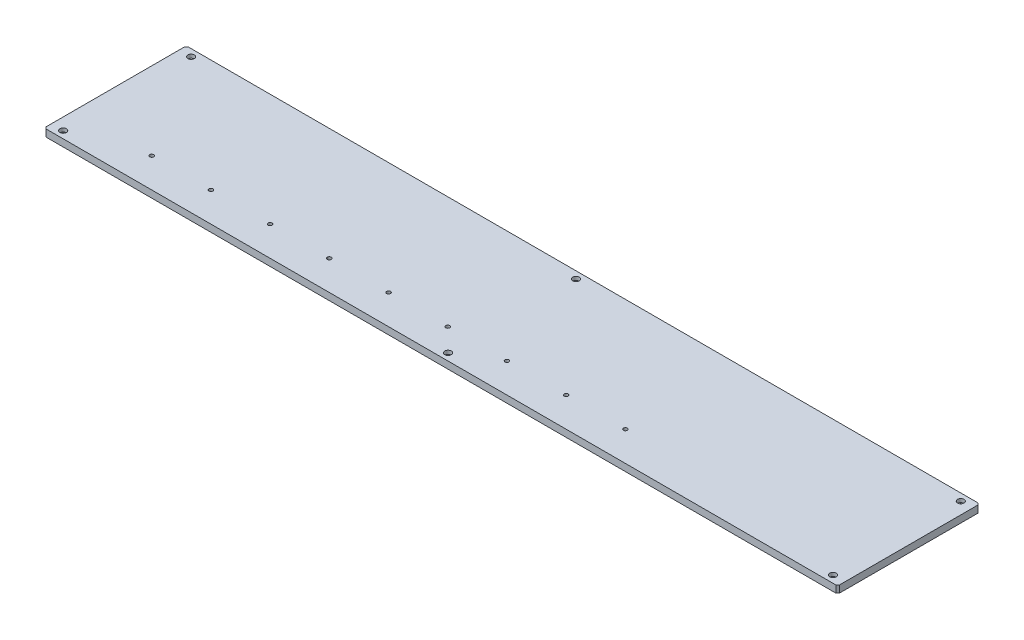
SolidWorks part; units mm, degrees
ref_plane "Front" through (0, 0, 0) normal (0, 0, 1) x (1, 0, 0)
ref_plane "Top" through (0, 0, 0) normal (0, 1, 0) x (1, 0, 0)
ref_plane "Right" through (0, 0, 0) normal (1, 0, 0) x (0, 0, -1)
sketch "Sketch1" plane through (0, 0, 0) normal (0, 1, 0) x (1, 0, 0)
  line L1 (-63.4773, 0) -> (1030.8242, 0) construction
  line L3 (0, -120) -> (1340, -120)
  line L4 (0, -120) -> (0, 120)
  line L5 (0, 120) -> (1340, 120)
  line L6 (1340, -120) -> (1340, 120)
  dimension "D1" = 1340
  dimension "D2" = 240
extrude "Boss-Extrude1" add sketch "Sketch1" along normal blind 12
hole_wizard "CBORE for M6 Socket Head Cap Screw1" positions "Sketch3" profile "Sketch2" counterbore size "M6" standard "JIS" end condition through all
sketch "Sketch3" plane through (0, 12, 0) normal (0, 1, 0) x (-1, 0, 0)
  line L1 (0, -120) -> (0, 120) construction
  line L4 (-1340, 120) -> (-1340, -120) construction
  line L7 (-1340, -120) -> (0, -120) construction
  line L8 (24.1675, 0) -> (-220.0945, 0) construction
  line L10 (0, 120) -> (-1340, 120) construction
  point P0 (-20, 108)
  point P1 (-20, -108)
  point P3 (-670, 108)
  point P5 (-670, -108)
  point P37 (-1320, 108)
  point P38 (-1320, -108)
  dimension "D1" = 12
  dimension "D2" = 20
  dimension "D3" = 216
  dimension "D4" = 650
  dimension "D5" = 12
  dimension "D6" = 670
  dimension "D7" = 650
sketch "Sketch2" plane through (20, 12, 108) normal (1, 0, 0) x (0, 0, 1)
  line L0 (0, 0) -> (0, 12)
  line L1 (0, 12) -> (3.3, 12)
  line L3 (3.3, 12) -> (3.3, 6)
  line L4 (3.3, 6) -> (5.5, 6)
  line L5 (5.5, 6) -> (5.5, 0)
  line L7 (5.5, 0) -> (0, 0)
  line L11 (0, -6.35) -> (0, 107.95) construction
  dimension "通し穴の直径" = 6.6
  dimension "通し穴の深さ" = 12
  dimension "座ぐり穴の直径" = 11
  dimension "座ぐり穴の深さ" = 6
hole_wizard "CBORE for M6 Socket Head Cap Screw2" positions "Sketch5" profile "Sketch4" counterbore size "M6" standard "JIS" end condition through all
sketch "Sketch5" plane through (0, 0, 0) normal (0, -1, 0) x (1, 0, 0)
  line L0 (0, -120) -> (0, 120) construction
  line L1 (0, 120) -> (1340, 120) construction
  point P0 (131.5, 70)
  point P1 (231.5, 70)
  point P3 (331.5, 70)
  point P5 (431.5, 70)
  point P7 (531.5, 70)
  point P9 (631.5, 70)
  point P15 (731.5, 70)
  point P17 (831.5, 70)
  point P19 (931.5, 70)
  dimension "D1" = 131.5
  dimension "D2" = 100
  dimension "D3" = 100
  dimension "D4" = 100
  dimension "D5" = 100
  dimension "D6" = 100
  dimension "D7" = 100
  dimension "D8" = 100
  dimension "D9" = 100
  dimension "D10" = 50
sketch "Sketch4" plane through (131.5, 0, 70) normal (1, 0, 0) x (0, 0, -1)
  line L0 (0, 0) -> (0, 12)
  line L1 (0, 12) -> (3.3, 12)
  line L3 (3.3, 12) -> (3.3, 6)
  line L4 (3.3, 6) -> (5.5, 6)
  line L5 (5.5, 6) -> (5.5, 0)
  line L7 (5.5, 0) -> (0, 0)
  line L11 (0, -6.35) -> (0, 107.95) construction
  dimension "通し穴の直径" = 6.6
  dimension "通し穴の深さ" = 12
  dimension "座ぐり穴の直径" = 11
  dimension "座ぐり穴の深さ" = 6
hole_wizard "CBORE for M5 Socket Head Cap Screw1" positions "Sketch7" profile "Sketch6" counterbore size "M5" standard "JIS"
sketch "Sketch7" plane through (0, 0, 0) normal (0, -1, 0) x (1, 0, 0)
  line L1 (1340, -120) -> (0, -120) construction
  line L2 (0, -120) -> (0, 120) construction
  point P0 (945, -102.5)
  point P1 (945, -52.5)
  point P3 (645, -102.5)
  point P5 (645, -52.5)
  point P7 (325, -102.5)
  point P9 (325, -52.5)
  dimension "D1" = 325
  dimension "D2" = 320
  dimension "D3" = 620
  dimension "D4" = 17.5
  dimension "D5" = 50
sketch "Sketch6" plane through (945, 0, -102.5) normal (1, 0, 0) x (0, 0, -1)
  line L0 (0, 0) -> (0, 12)
  line L1 (0, 12) -> (2.75, 12)
  line L3 (2.75, 12) -> (2.75, 5)
  line L4 (2.75, 5) -> (5, 5)
  line L5 (5, 5) -> (5, 0)
  line L7 (5, 0) -> (0, 0)
  line L11 (0, -6.35) -> (0, 107.95) construction
  dimension "通し穴の直径" = 5.5
  dimension "通し穴の深さ" = 12
  dimension "座ぐり穴の直径" = 10
  dimension "座ぐり穴の深さ" = 5
chamfer "Chamfer1" distance 3 angle 45 4 edges at (1340, 6, -120) (1340, 6, 120) (0, 6, -120) (0, 6, 120)
